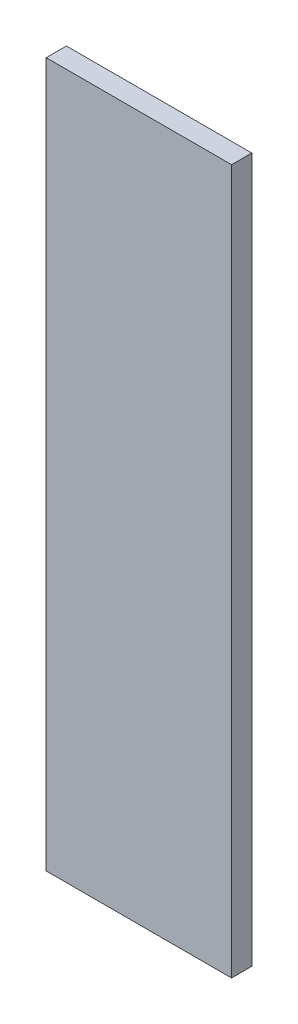
SolidWorks part; units mm, degrees
ref_plane "Front Plane" through (0, 0, 0) normal (0, 0, 1) x (1, 0, 0)
ref_plane "Top Plane" through (0, 0, 0) normal (0, 1, 0) x (1, 0, 0)
ref_plane "Right Plane" through (0, 0, 0) normal (1, 0, 0) x (0, 0, -1)
sketch "Sketch1" plane through (0, 0, 0) normal (0, 0, 1) x (1, 0, 0)
  line L1 (82.5, -313.5) -> (-82.5, -313.5)
  line L2 (82.5, -313.5) -> (82.5, 313.5)
  line L3 (82.5, 313.5) -> (-82.5, 313.5)
  line L4 (-82.5, -313.5) -> (-82.5, 313.5)
  line L5 (82.5, -313.5) -> (-82.5, 313.5) construction
  line L6 (82.5, 313.5) -> (-82.5, -313.5) construction
  point P0 (0, 0)
  dimension "D1" = 627
  dimension "D2" = 165
extrude "Boss-Extrude1" add sketch "Sketch1" along normal blind 18
equation "\"H_DSP\"=18"
equation "\"D1@Boss-Extrude1\"=\"H_DSP\""
